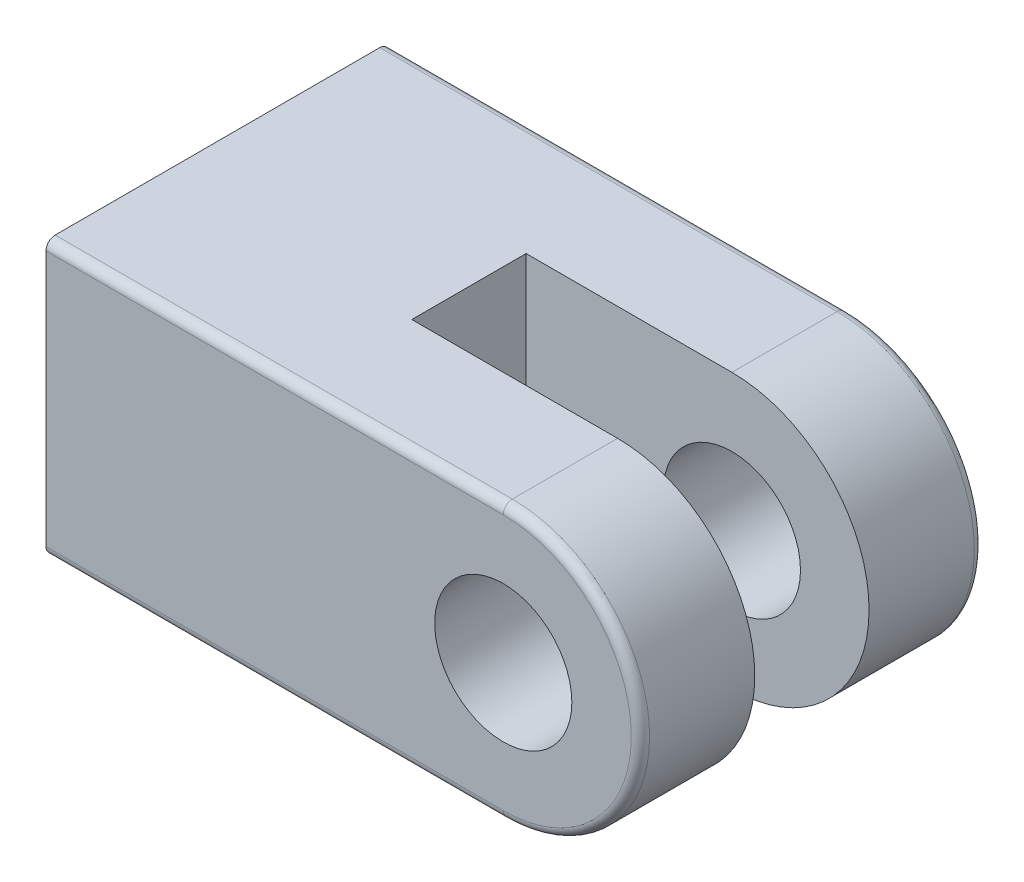
SolidWorks part; units mm, degrees
ref_plane "Front Plane" through (0, 0, 0) normal (0, 0, 1) x (1, 0, 0)
ref_plane "Top Plane" through (0, 0, 0) normal (0, 1, 0) x (1, 0, 0)
ref_plane "Right Plane" through (0, 0, 0) normal (1, 0, 0) x (0, 0, -1)
sketch "Sketch1" plane through (0, 0, 0) normal (0, 0, 1) x (1, 0, 0)
  line L0 (0, 7.62) -> (-25.4, 7.62)
  line L1 (-25.4, 7.62) -> (-25.4, -7.62)
  line L2 (-25.4, -7.62) -> (0, -7.62)
  arc A0 (0, -7.62) -> (0, 7.62) centre (0, 0) ccw
  dimension "D1" = 7.62
  dimension "D2" = 25.4
extrude "Boss-Extrude1" add sketch "Sketch1" along normal blind 19.05
sketch "Sketch2" plane through (0, 0, 0) normal (0, 1, 0) x (1, 0, 0)
  line L0 (7.62, -6.35) -> (-11.43, -6.35)
  line L1 (7.62, -19.05) -> (7.62, 0) construction
  line L2 (-11.43, -6.35) -> (-11.43, -12.7)
  line L3 (-11.43, -12.7) -> (7.62, -12.7)
  line L4 (7.62, -12.7) -> (7.62, -6.35)
  line L5 (7.62, 0) -> (0, 0) construction
  dimension "D1" = 19.05
  dimension "D2" = 6.35
  dimension "D3" = 6.35
extrude "Cut-Extrude1" cut sketch "Sketch2" against normal through all and the other way through all
sketch "Sketch3" plane through (0, 0, 19.05) normal (0, 0, 1) x (1, 0, 0)
  circle A0 centre (0, 0) radius 3.81
  dimension "D1" = 3.81
extrude "Cut-Extrude2" cut sketch "Sketch3" against normal through all
fillet "Fillet1" radius 0.508 6 edges at (-12.7, -7.62, 0) (-12.7, 7.62, 0) (-12.7, -7.62, 19.05) (-12.7, 7.62, 19.05) (7.62, 0, 0) (7.62, 0, 19.05)
